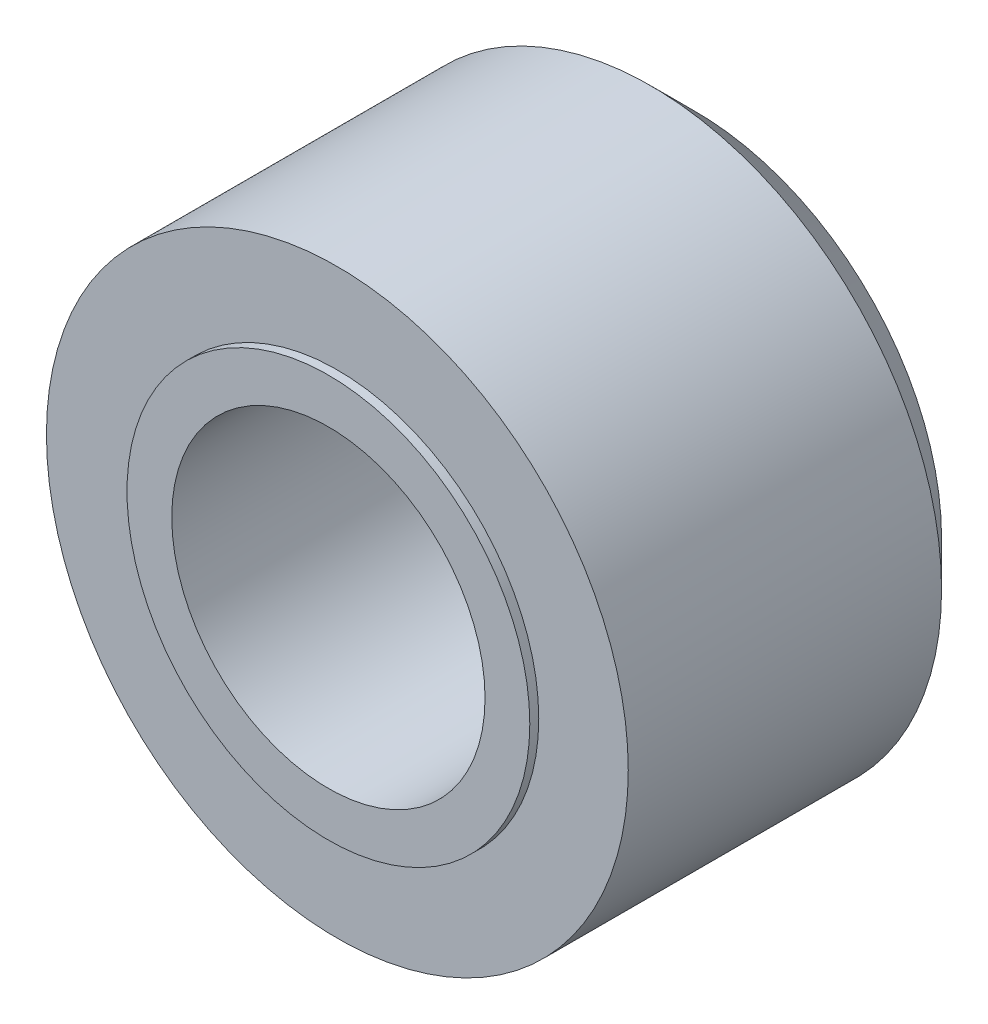
SolidWorks part; units mm, degrees
ref_plane "Front Plane" through (0, 0, 0) normal (0, 0, 1) x (1, 0, 0)
ref_plane "Top Plane" through (0, 0, 0) normal (0, 1, 0) x (1, 0, 0)
ref_plane "Right Plane" through (0, 0, 0) normal (1, 0, 0) x (0, 0, -1)
sketch "Sketch1" plane through (0, 0, 0) normal (0, 0, 1) x (1, 0, 0)
  circle A0 centre (0, 0) radius 3.25
  circle A1 centre (0, 0) radius 1.75
  dimension "D1" = 6.5
  dimension "D2" = 3.5
extrude "Boss-Extrude1" add sketch "Sketch1" along normal blind 4
sketch "Sketch2" plane through (0, 0, 4) normal (0, 0, 1) x (1, 0, 0)
  circle A0 centre (0, 0) radius 1.75
  circle A1 centre (0, 0) radius 2.25
  dimension "D1" = 4.5
extrude "Boss-Extrude2" add sketch "Sketch2" along normal blind 0.1
chamfer "Chamfer1" distance 0.5 angle 45 1 edges at (3.25, 0, 0)
